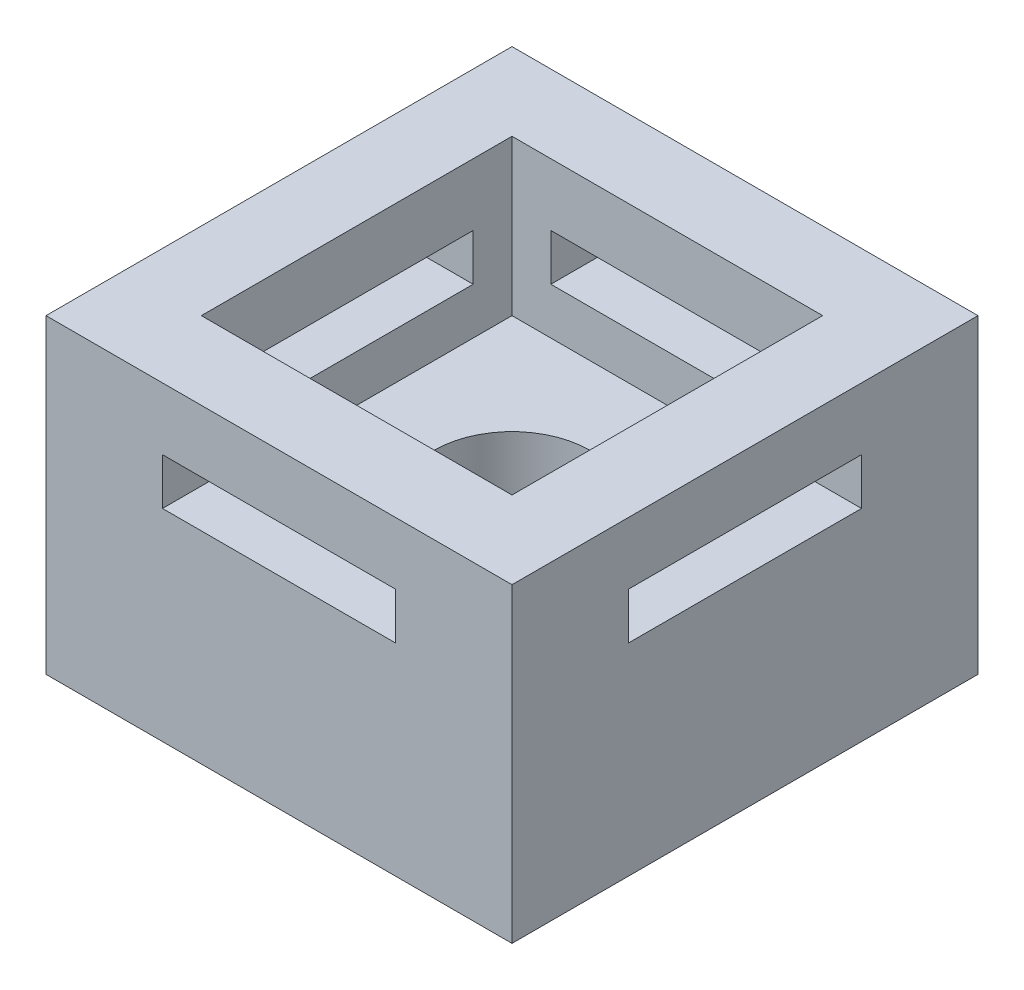
SolidWorks part; units mm, degrees
ref_plane "Front Plane" through (0, 0, 0) normal (0, 0, 1) x (1, 0, 0)
ref_plane "Top Plane" through (0, 0, 0) normal (0, 1, 0) x (1, 0, 0)
ref_plane "Right Plane" through (0, 0, 0) normal (1, 0, 0) x (0, 0, -1)
sketch "Sketch1" plane through (0, 0, 0) normal (0, 1, 0) x (1, 0, 0)
  line L1 (0, 0) -> (15.24, 0)
  line L2 (0, 0) -> (0, 15.24)
  line L3 (0, 15.24) -> (15.24, 15.24)
  line L4 (15.24, 0) -> (15.24, 15.24)
extrude "Boss-Extrude1" add sketch "Sketch1" along normal blind 10.16
sketch "Sketch2" plane through (0, 0, 0) normal (0, 1, 0) x (1, 0, 0)
  circle A0 centre (7.62, 7.62) radius 2.54
extrude "Cut-Extrude3" cut sketch "Sketch2" along normal blind 10.16
sketch "Sketch5" plane through (0, 10.16, 0) normal (0, 1, 0) x (1, 0, 0)
  line L1 (2.54, 12.7) -> (12.7, 12.7)
  line L2 (2.54, 12.7) -> (2.54, 2.54)
  line L3 (2.54, 2.54) -> (12.7, 2.54)
  line L4 (12.7, 12.7) -> (12.7, 2.54)
extrude "Cut-Extrude5" cut sketch "Sketch5" against normal blind 5.08
sketch "Sketch7" plane through (0, 0, 0) normal (0, 0, 1) x (1, 0, 0)
  line L1 (3.81, 8.128) -> (11.43, 8.128)
  line L2 (3.81, 8.128) -> (3.81, 6.604)
  line L3 (3.81, 6.604) -> (11.43, 6.604)
  line L4 (11.43, 8.128) -> (11.43, 6.604)
extrude "Cut-Extrude6" cut sketch "Sketch7" against normal blind 15.24
sketch "Sketch8" plane through (15.24, 0, 0) normal (1, 0, 0) x (0, 0, -1)
  line L1 (3.81, 8.128) -> (11.43, 8.128)
  line L2 (3.81, 8.128) -> (3.81, 6.604)
  line L3 (3.81, 6.604) -> (11.43, 6.604)
  line L4 (11.43, 8.128) -> (11.43, 6.604)
extrude "Cut-Extrude7" cut sketch "Sketch8" against normal blind 15.24
